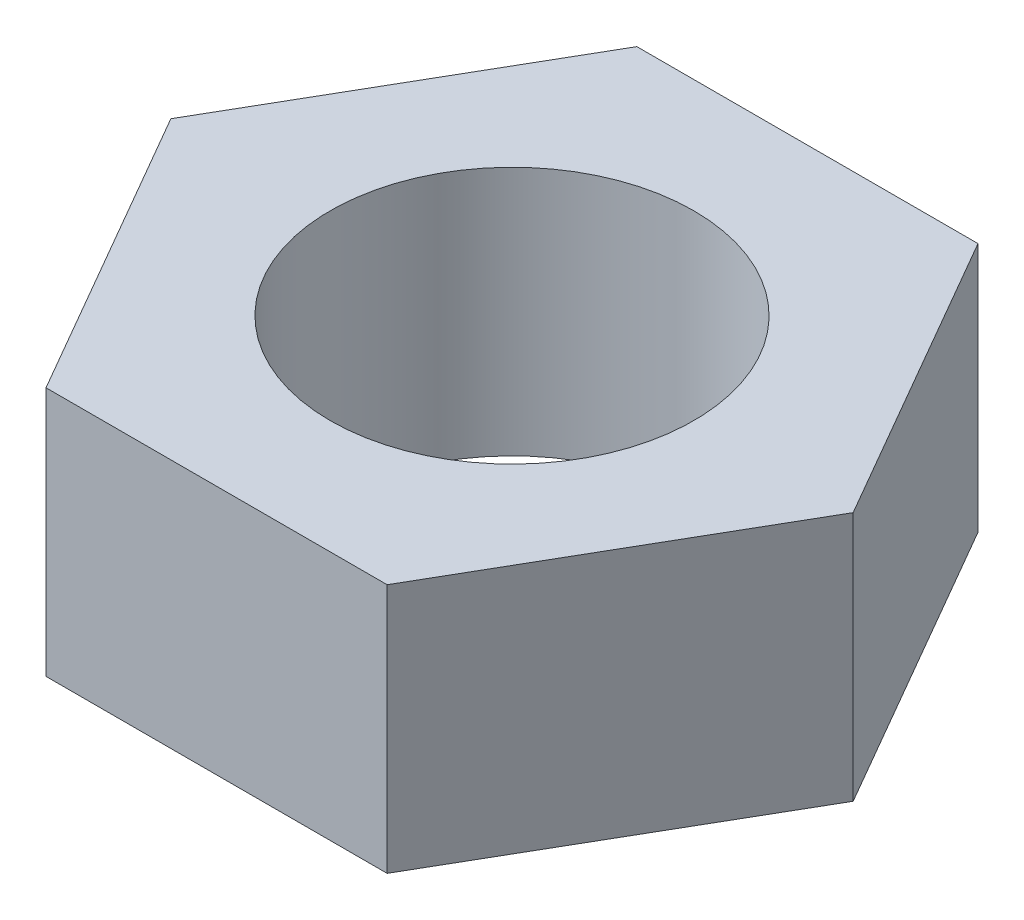
SolidWorks part; units mm, degrees
material "Plain Carbon Steel"
ref_plane "Front Plane" through (0, 0, 0) normal (0, 0, 1) x (1, 0, 0)
ref_plane "Top Plane" through (0, 0, 0) normal (0, 1, 0) x (1, 0, 0)
ref_plane "Right Plane" through (0, 0, 0) normal (1, 0, 0) x (0, 0, -1)
sketch "Sketch1" plane through (0, 0, 0) normal (0, 1, 0) x (1, 0, 0)
  line L1 (-3.7528, 6.5) -> (-7.5056, 0)
  line L2 (-7.5056, 0) -> (-3.7528, -6.5)
  line L3 (-3.7528, -6.5) -> (3.7528, -6.5)
  line L4 (3.7528, -6.5) -> (7.5056, 0)
  line L5 (7.5056, 0) -> (3.7528, 6.5)
  line L6 (3.7528, 6.5) -> (-3.7528, 6.5)
  circle A0 centre (0, 0) radius 4
  circle A1 centre (0, 0) radius 6.5 construction
  dimension "D1" = 8
  dimension "D2" = 13
extrude "Boss-Extrude1" add sketch "Sketch1" along normal blind 5.5
